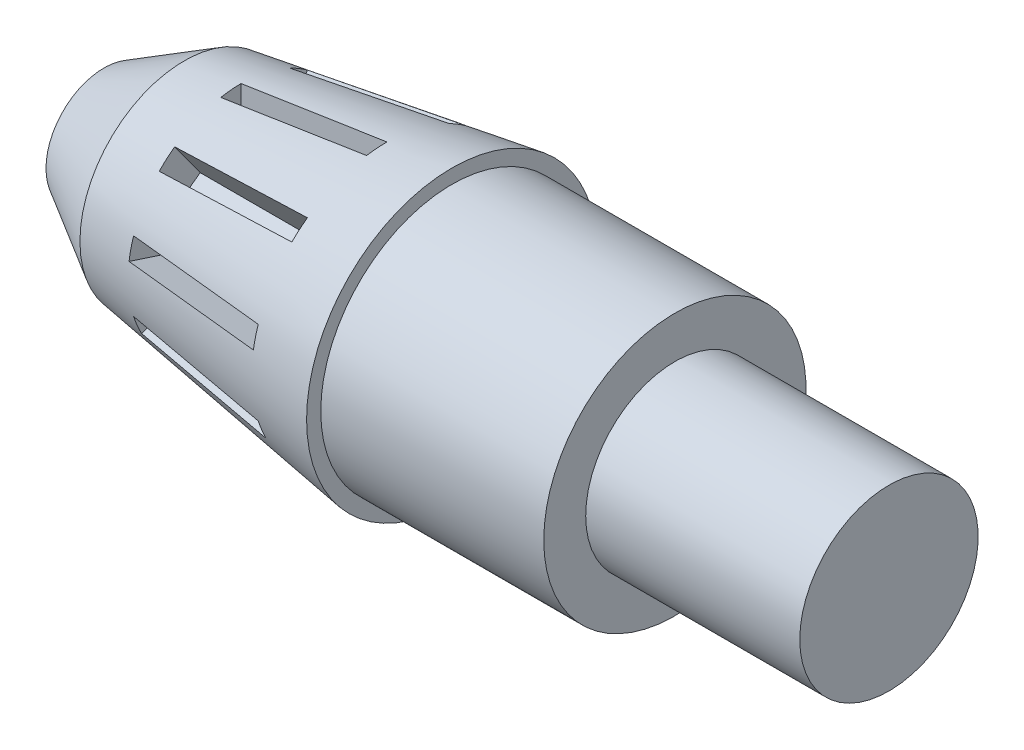
SolidWorks part; units mm, degrees
ref_plane "Front Plane" through (0, 0, 0) normal (0, 0, 1) x (1, 0, 0)
ref_plane "Top Plane" through (0, 0, 0) normal (0, 1, 0) x (1, 0, 0)
ref_plane "Right Plane" through (0, 0, 0) normal (1, 0, 0) x (0, 0, -1)
sketch "Sketch1" plane through (0, 0, 0) normal (0, 0, 1) x (1, 0, 0)
  line L0 (-45, 22.5) -> (-20, 22.5)
  line L1 (0, 35.3963) -> (0, -22.2256) construction
  line L2 (0, 27) -> (-75, 22.15) construction
  line L3 (4, 7.8) -> (4, 17.8)
  line L4 (4, 17.8) -> (-20, 17.8)
  line L5 (-20, 17.8) -> (-20, 22.5)
  line L7 (-45, 22.5) -> (-45, 24.09)
  line L8 (-45, 24.09) -> (-75, 19.4993)
  line L10 (-59, 7.8) -> (4, 7.8)
  line L11 (-75, 19.4993) -> (-84, 14.3032)
  line L12 (-84, 14.3032) -> (-84, 13)
  line L13 (-75, 22.15) -> (-75, 5.3197) construction
  line L14 (-84, 13) -> (-59, 13)
  line L15 (-59, 13) -> (-59, 7.8)
  dimension "D2" = 75
  dimension "D3" = 5.2
  dimension "D4" = 4
  dimension "D5" = 10
  dimension "D7" = 20
  dimension "D8" = 45
  dimension "D9" = 5
  dimension "D10" = 9
  dimension "D13" = 25
revolve "Revolve1" add sketch "Sketch1" angle 360 about L10
sketch "Sketch2" plane through (0, 0, 0) normal (0, 1, 0) x (1, 0, 0)
  line L1 (-68.6308, 0) -> (-52.2797, 0)
  line L2 (-68.6308, 0) -> (-68.6308, 2.2863)
  line L3 (-68.6308, 2.2863) -> (-52.2797, 2.2863)
  line L4 (-52.2797, 0) -> (-52.2797, 2.2863)
extrude "Cut-Extrude2" cut sketch "Sketch2" against normal blind 8
pattern_circular "CirPattern1" count 10 over 360 about axis through (0, 7.8, 0) along (1, 0, 0) of "Cut-Extrude2"
sketch "Sketch3" plane through (-59, 0, 0) normal (-1, 0, 0) x (0, 0, 1)
  line L0 (0, 7.8) -> (0, 2.6)
  line L1 (-1.7911, 12.6818) -> (-0.8611, 10.147)
  line L2 (1.1484, 10.0206) -> (2.3886, 12.4189)
  circle A0 centre (0, 7.8) radius 5.2 construction
  arc A1 (1.1484, 10.0206) -> (-0.8611, 10.147) centre (0, 7.8) ccw
  arc A2 (2.3886, 12.4189) -> (-1.7911, 12.6818) centre (0, 7.8) ccw
  circle M6 centre (0, 7.8) radius 5.2
  dimension "D1" = 5
extrude "Boss-Extrude2" add sketch "Sketch3" along normal blind 23 contours A1 L2 L1 M6
pattern_circular "CirPattern2" count 3 over 360 about axis through (0, 7.8, 0) along (1, 0, 0) of "Boss-Extrude2"
